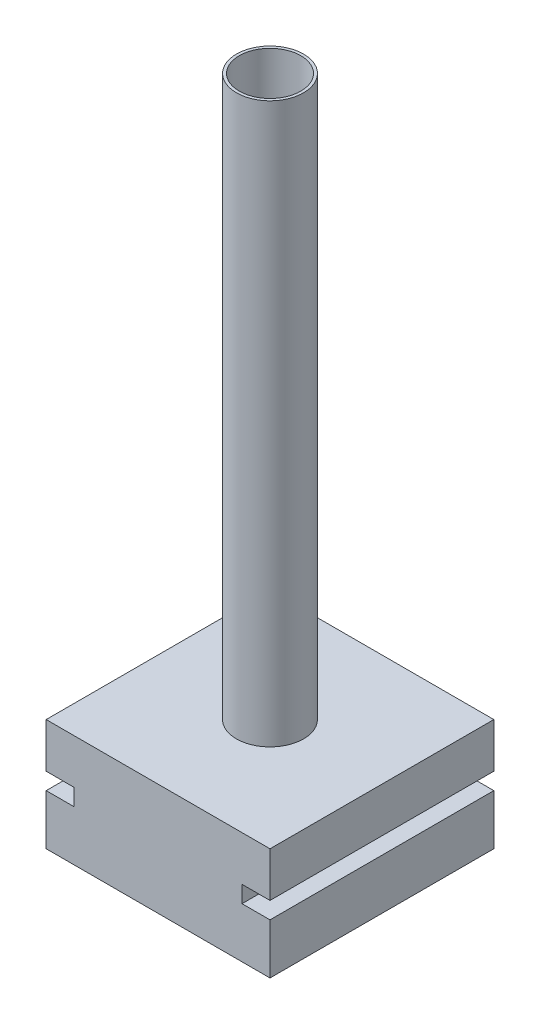
SolidWorks part; units mm, degrees
ref_plane "Front Plane" through (0, 0, 0) normal (0, 0, 1) x (1, 0, 0)
ref_plane "Top Plane" through (0, 0, 0) normal (0, 1, 0) x (1, 0, 0)
ref_plane "Right Plane" through (0, 0, 0) normal (1, 0, 0) x (0, 0, -1)
sketch "Sketch1" plane through (0, 0, 0) normal (0, 1, 0) x (1, 0, 0)
  line L1 (200, -200) -> (-200, -200)
  line L2 (200, -200) -> (200, 200)
  line L3 (200, 200) -> (-200, 200)
  line L4 (-200, -200) -> (-200, 200)
  line L5 (200, -200) -> (-200, 200) construction
  line L6 (200, 200) -> (-200, -200) construction
  point P0 (0, 0)
  dimension "D1" = 400
  dimension "D2" = 400
extrude "Boss-Extrude1" add sketch "Sketch1" along normal blind 200
sketch "Sketch2" plane through (0, 200, 0) normal (0, 1, 0) x (1, 0, 0)
  circle A1 centre (0, 0) radius 55
  circle A2 centre (0, 0) radius 60
  dimension "D1" = 5
extrude "Boss-Extrude2" add sketch "Sketch2" along normal blind 1000
sketch "Sketch3" plane through (0, 0, -200) normal (0, 0, -1) x (-1, 0, 0)
  line L0 (-200, 120) -> (-200, 90)
  line L1 (-200, 200) -> (-200, 0) construction
  line L2 (-200, 90) -> (-150, 90)
  line L3 (-150, 90) -> (-150, 120)
  line L4 (-150, 120) -> (-200, 120)
  line L5 (0, 200) -> (0, 0) construction
  line L6 (-200, 200) -> (200, 200) construction
  line L7 (200, 120) -> (200, 90)
  line L8 (200, 90) -> (150, 90)
  line L9 (150, 90) -> (150, 120)
  line L10 (150, 120) -> (200, 120)
  dimension "D2" = 50
  dimension "D3" = 30
extrude "Cut-Extrude1" cut sketch "Sketch3" against normal blind 584
